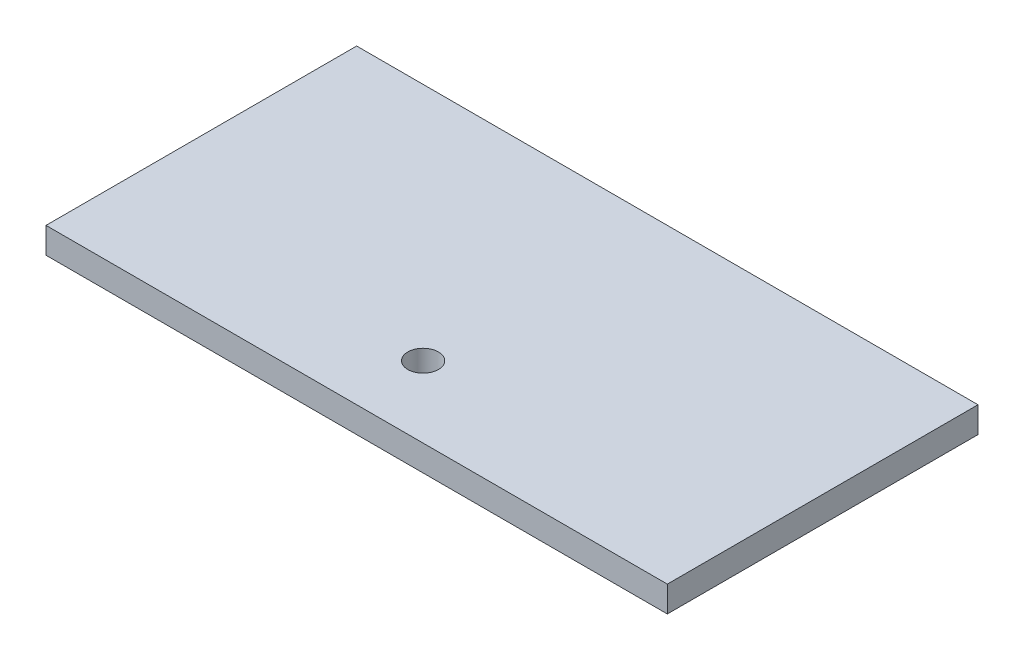
SolidWorks part; units mm, degrees
ref_plane "Front Plane" through (0, 0, 0) normal (0, 0, 1) x (1, 0, 0)
ref_plane "Top Plane" through (0, 0, 0) normal (0, 1, 0) x (1, 0, 0)
ref_plane "Right Plane" through (0, 0, 0) normal (1, 0, 0) x (0, 0, -1)
sketch "Sketch1" plane through (0, 0, 0) normal (0, 1, 0) x (1, 0, 0)
  line L1 (0, 0) -> (609.6, 0)
  line L2 (0, 0) -> (0, 304.8)
  line L3 (0, 304.8) -> (609.6, 304.8)
  line L4 (609.6, 0) -> (609.6, 304.8)
  dimension "D1" = 609.6
  dimension "D2" = 304.8
extrude "Boss-Extrude1" add sketch "Sketch1" along normal blind 25.4
sketch "Sketch2" plane through (0, 25.4, 0) normal (0, 1, 0) x (1, 0, 0)
  line L1 (0, 0) -> (300, 0)
  line L2 (0, 0) -> (0, 70)
  line L3 (0, 70) -> (300, 70)
  line L4 (300, 0) -> (300, 70)
  circle A0 centre (300, 70) radius 15
  dimension "D1" = 300
  dimension "D2" = 70
extrude "Cut-Extrude1" cut sketch "Sketch2" against normal blind 25.4 contours A0
